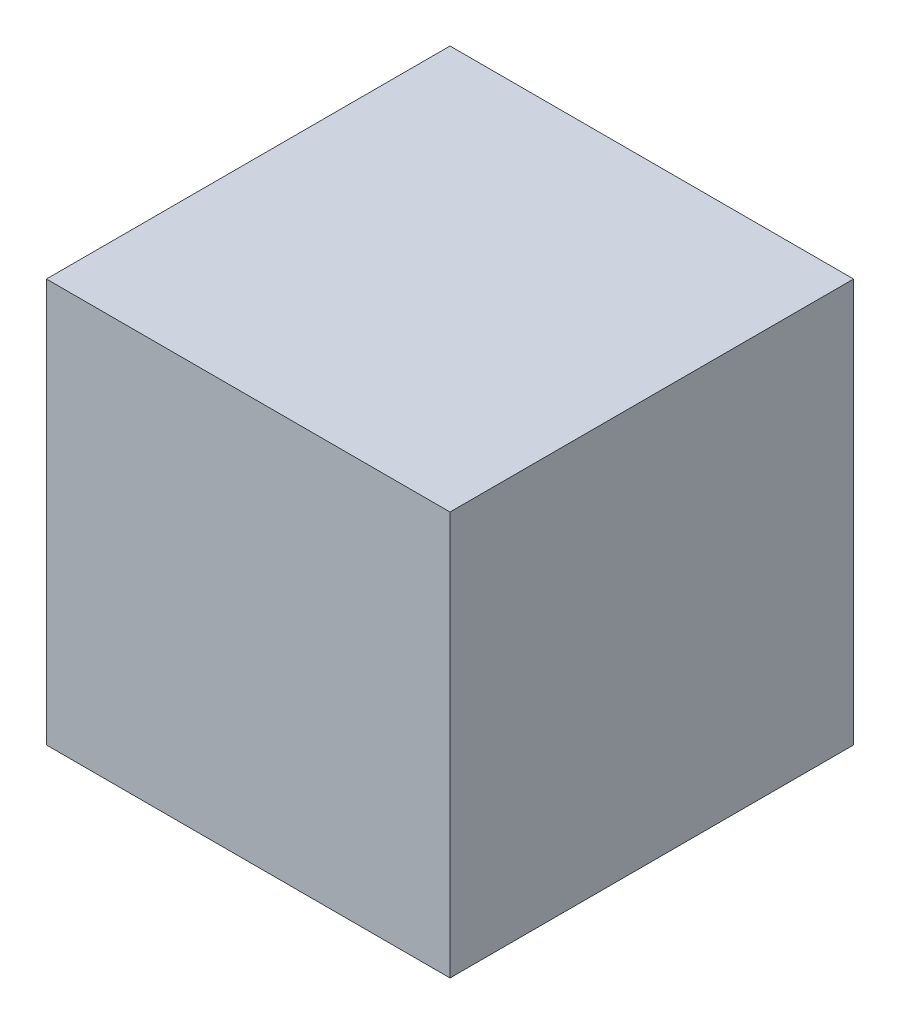
SolidWorks part; units mm, degrees
ref_plane "Front Plane" through (0, 0, 0) normal (0, 0, 1) x (1, 0, 0)
ref_plane "Top Plane" through (0, 0, 0) normal (0, 1, 0) x (1, 0, 0)
ref_plane "Right Plane" through (0, 0, 0) normal (1, 0, 0) x (0, 0, -1)
sketch "Sketch1" plane through (0, 0, 0) normal (0, 1, 0) x (1, 0, 0)
  line L1 (0, 0) -> (10, 0)
  line L2 (0, 0) -> (0, 10)
  line L3 (0, 10) -> (10, 10)
  line L4 (10, 0) -> (10, 10)
  dimension "D1" = 10
  dimension "D2" = 10
extrude "Boss-Extrude1" add sketch "Sketch1" along normal blind 10
